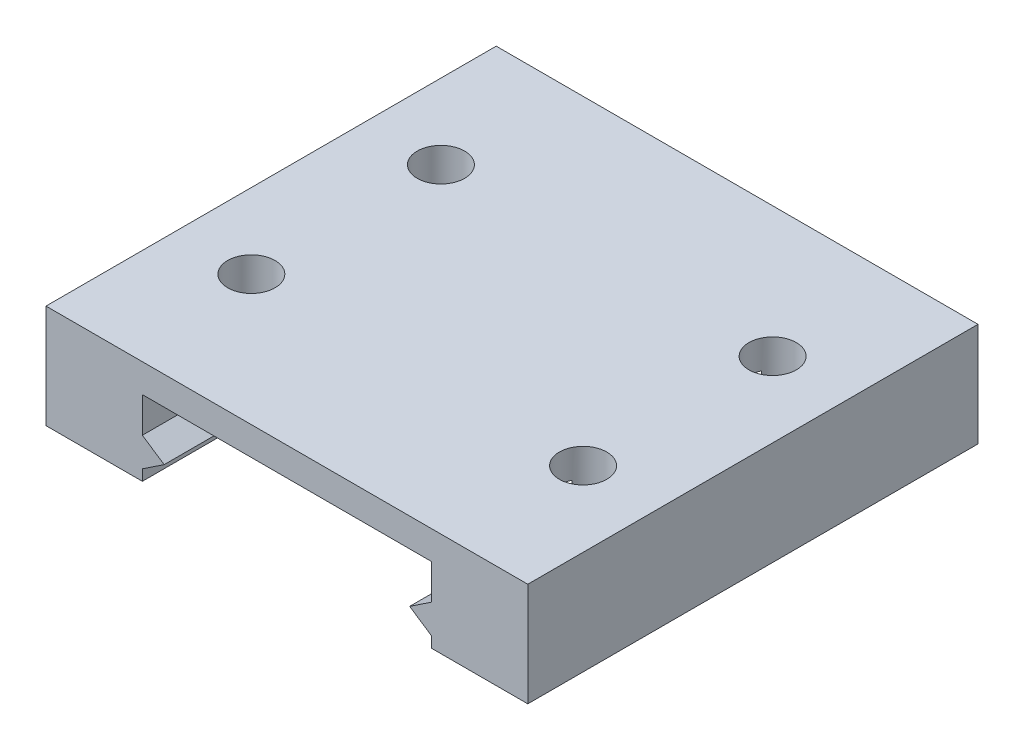
SolidWorks part; units mm, degrees
ref_plane "Front Plane" through (0, 0, 0) normal (0, 0, 1) x (1, 0, 0)
ref_plane "Top Plane" through (0, 0, 0) normal (0, 1, 0) x (1, 0, 0)
ref_plane "Right Plane" through (0, 0, 0) normal (1, 0, 0) x (0, 0, -1)
sketch "Sketch1" plane through (0, 0, 0) normal (0, 0, 1) x (1, 0, 0)
  line L11 (-9.15, -1.1056) -> (-9.15, -0.4197)
  line L12 (-9.15, -0.4197) -> (-7.7704, 0.5)
  line L13 (-7.7704, 0.5) -> (-9.15, 1.4197)
  line L14 (-9.15, 1.4197) -> (-9.15, 3.65)
  line L15 (-9.15, 3.65) -> (9.15, 3.65)
  line L16 (9.15, 3.65) -> (9.15, 1.4197)
  line L17 (9.15, 1.4197) -> (7.7704, 0.5)
  line L18 (7.7704, 0.5) -> (9.15, -0.4197)
  line L19 (9.15, -0.4197) -> (9.15, -1.1056)
  line L21 (-15.25, 5.4529) -> (15.25, 5.4529)
  line L22 (-15.25, 5.4529) -> (-15.25, -1.1056)
  line L23 (-15.25, -1.1056) -> (-9.15, -1.1056)
  line L24 (9.15, -1.1056) -> (15.25, -1.1056)
  line L25 (15.25, -1.1056) -> (15.25, 5.4529)
  point P38 (0, 5.4529)
  dimension "D2" = 30.5
extrude "Boss-Extrude1" add sketch "Sketch1" against normal blind 28.5
sketch "Sketch2" plane through (0, 5.4529, 0) normal (0, 1, 0) x (1, 0, 0)
  circle A0 centre (-10.5, 8.25) radius 1.5
  circle A1 centre (-10.5, 20.25) radius 1.5
  circle A2 centre (10.5, 20.25) radius 1.5
  circle A3 centre (10.5, 8.25) radius 1.5
  point P14 (-10.5, 20.25)
  point P15 (10.5, 20.25)
  point P16 (10.5, 8.25)
  point P17 (-10.5, 8.25)
  dimension "D1" = 3
extrude "Cut-Extrude1" cut sketch "Sketch2" against normal blind 3
